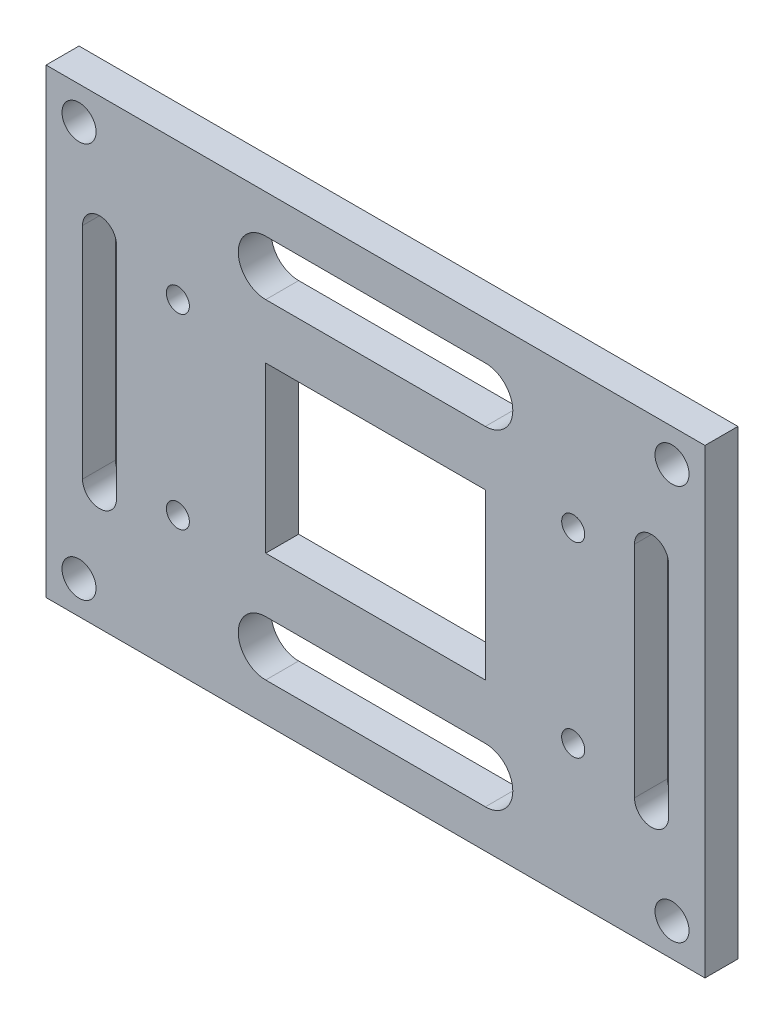
SolidWorks part; units mm, degrees
ref_plane "前视基准面" through (0, 0, 0) normal (0, 0, 1) x (1, 0, 0)
ref_plane "上视基准面" through (0, 0, 0) normal (0, 1, 0) x (1, 0, 0)
ref_plane "右视基准面" through (0, 0, 0) normal (1, 0, 0) x (0, 0, -1)
sketch "草图1" plane through (0, 0, 0) normal (0, 0, 1) x (1, 0, 0)
  line L0 (55, 0) -> (-55, 0) construction
  line L1 (-30, 21) -> (30, 21)
  line L2 (-30, 21) -> (-30, -21)
  line L3 (-30, -21) -> (30, -21)
  line L4 (30, 21) -> (30, -21)
  line L5 (-30, 21) -> (30, -21) construction
  line L6 (-30, -21) -> (30, 21) construction
  line L7 (-10, 7.5) -> (10, 7.5)
  line L8 (-10, 7.5) -> (-10, -7.5)
  line L9 (-10, -7.5) -> (10, -7.5)
  line L10 (10, 7.5) -> (10, -7.5)
  line L11 (-10, 7.5) -> (10, -7.5) construction
  line L12 (-10, -7.5) -> (10, 7.5) construction
  line L13 (0, -55) -> (0, 55) construction
  line L14 (-10, 15) -> (10, 15) construction
  line L15 (-10, 17.5) -> (10, 17.5)
  line L16 (-10, 12.5) -> (10, 12.5)
  line L17 (-10, -15) -> (10, -15) construction
  line L18 (-10, -17.5) -> (10, -17.5)
  line L19 (-10, -12.5) -> (10, -12.5)
  line L20 (-25.1333, 10) -> (-25.1333, -10) construction
  line L21 (-23.5833, 10) -> (-23.5833, -10)
  line L22 (-26.6833, 10) -> (-26.6833, -10)
  line L23 (25.1333, 10) -> (25.1333, -10) construction
  line L24 (23.5833, 10) -> (23.5833, -10)
  line L25 (26.6833, 10) -> (26.6833, -10)
  circle A0 centre (-18, -8.5) radius 1.05
  circle A1 centre (-18, 8.5) radius 1.05
  circle A2 centre (18, 8.5) radius 1.05
  circle A3 centre (18, -8.5) radius 1.05
  circle A4 centre (-27, -18) radius 1.55
  circle A5 centre (27, -18) radius 1.55
  circle A6 centre (27, 18) radius 1.55
  circle A7 centre (-27, 18) radius 1.55
  arc A8 (-10, 17.5) -> (-10, 12.5) centre (-10, 15) ccw
  arc A9 (10, 12.5) -> (10, 17.5) centre (10, 15) ccw
  arc A10 (-10, -17.5) -> (-10, -12.5) centre (-10, -15) cw
  arc A11 (10, -12.5) -> (10, -17.5) centre (10, -15) cw
  arc A12 (-23.5833, 10) -> (-26.6833, 10) centre (-25.1333, 10) ccw
  arc A13 (-26.6833, -10) -> (-23.5833, -10) centre (-25.1333, -10) ccw
  arc A14 (23.5833, 10) -> (26.6833, 10) centre (25.1333, 10) cw
  arc A15 (26.6833, -10) -> (23.5833, -10) centre (25.1333, -10) cw
  point P0 (0, 0)
  point P6 (0, 0)
  point P33 (0, 15)
  point P41 (0, -15)
  point P46 (-25.1333, 0)
  point P55 (25.1333, 0)
  dimension "D7" = 2.1
  dimension "D8" = 3.1
  dimension "D12" = 2.5
  dimension "D14" = 1.55
  dimension "D1" = 60
  dimension "D2" = 20
  dimension "D3" = 42
  dimension "D4" = 15
  dimension "D5" = 18
  dimension "D6" = 8.5
  dimension "D9" = 3
  dimension "D10" = 3
  dimension "D11" = 20
  dimension "D13" = 15
  dimension "D15" = 20
extrude "凸台-拉伸1" add sketch "草图1" along normal blind 3
